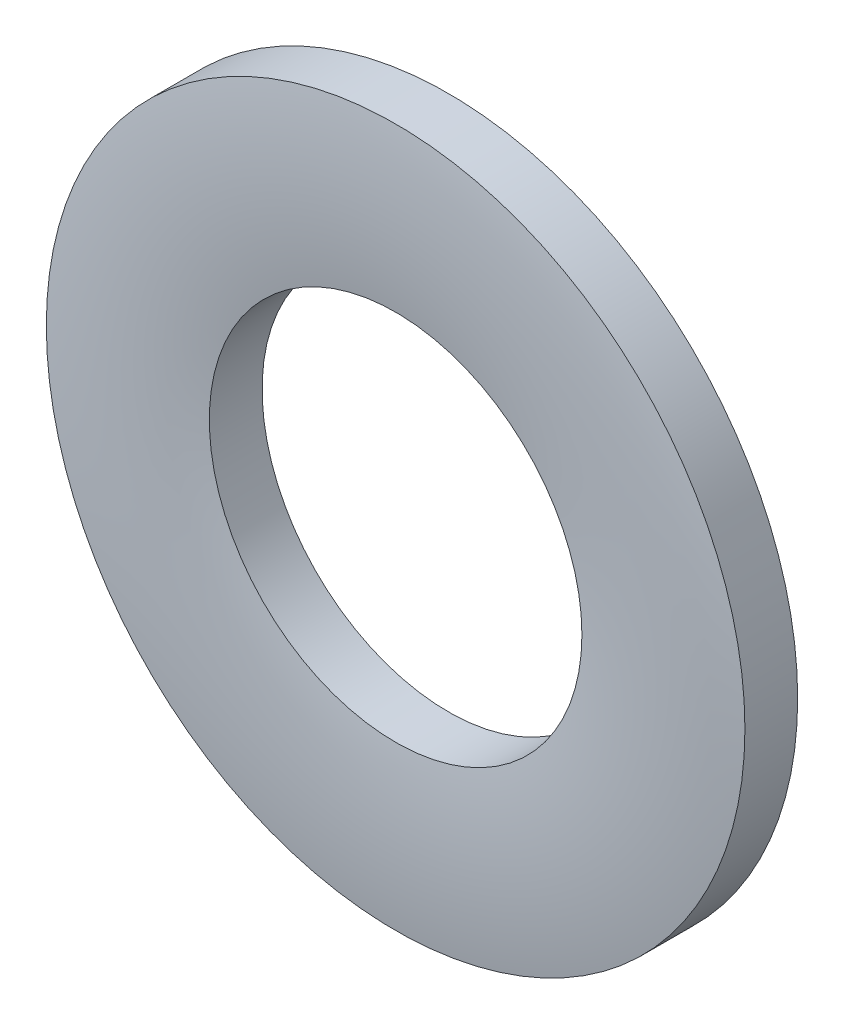
SolidWorks part; units mm, degrees
material "Stainless Steel (ferritic)"
ref_plane "Front Plane" through (0, 0, 0) normal (0, 0, 1) x (1, 0, 0)
ref_plane "Top Plane" through (0, 0, 0) normal (0, 1, 0) x (1, 0, 0)
ref_plane "Right Plane" through (0, 0, 0) normal (1, 0, 0) x (0, 0, -1)
sketch "Sketch1" plane through (0, 0, 0) normal (0, 0, 1) x (1, 0, 0)
  circle A0 centre (0, 0) radius 1.6
  circle A1 centre (0, 0) radius 3
  dimension "ID" = 3.2
  dimension "OD" = 6
sketch "Sketch2" plane through (0, 0, 0) normal (1, 0, 0) x (0, 0, -1)
  line L0 (-0.25, 3) -> (0.25, 3) construction
  line L1 (-0.25, 0) -> (0.25, 0) construction
  point P2 (0, 3)
  dimension "Thickness Range" = 0.5
sketch "Sketch3" plane through (0, 0, 0) normal (1, 0, 0) x (0, 0, -1)
  line L0 (0.25, 3) -> (-0.2031, 3)
  line L1 (0.25, 1.6) -> (-0.2031, 1.6)
  line L2 (0.25, 1.6) -> (0.25, 3)
  line L3 (-0.25, 3) -> (-0.25, 1.6) construction
  arc A0 (-0.2031, 1.6) -> (-0.2031, 3) centre (5.0029, 2.3) cw
  point P9 (0, 1.6)
  dimension "D1" = 0.0469
revolve "Revolve1" add sketch "Sketch3" angle 360 about L1
equation "\"D1@Sketch3\"=\"Thickness Range@Sketch2\"*.0937"
